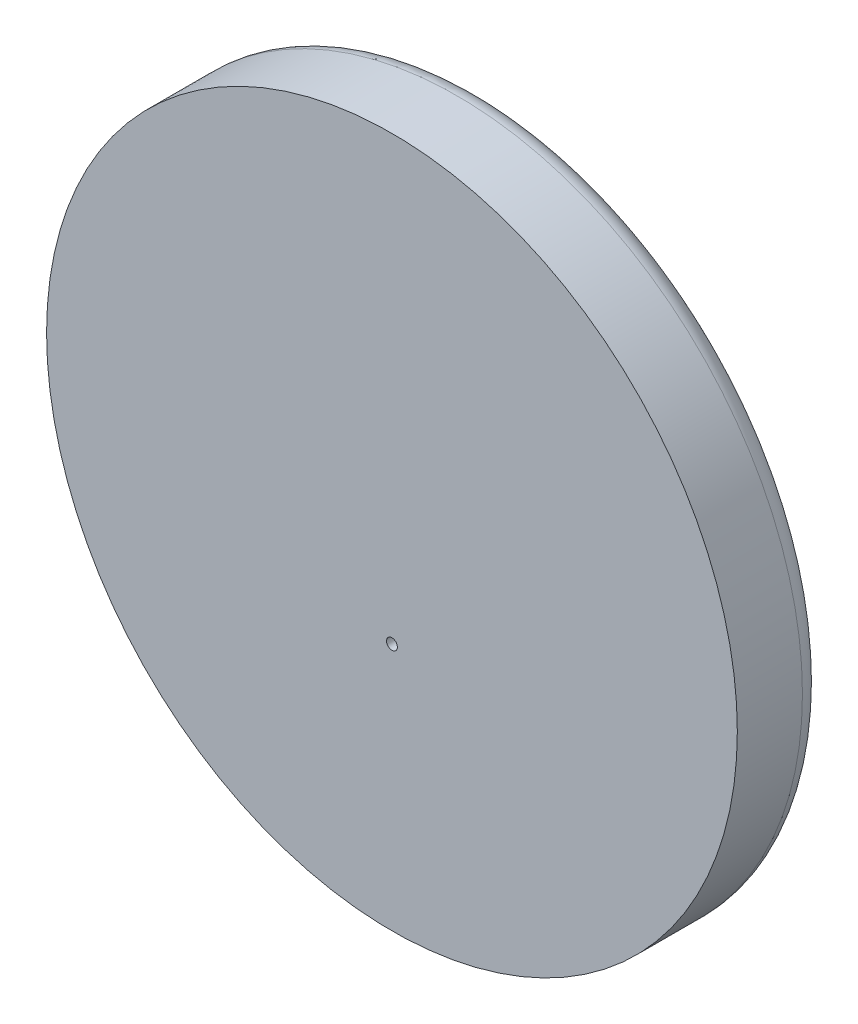
SolidWorks part; units mm, degrees
ref_plane "Front Plane" through (0, 0, 0) normal (0, 0, 1) x (1, 0, 0)
ref_plane "Top Plane" through (0, 0, 0) normal (0, 1, 0) x (1, 0, 0)
ref_plane "Right Plane" through (0, 0, 0) normal (1, 0, 0) x (0, 0, -1)
sketch "Sketch2" plane through (0, 0, 0) normal (0, 0, 1) x (1, 0, 0)
  circle A0 centre (0, 35.3882) radius 31.83
extrude "Boss-Extrude1" add sketch "Sketch2" along normal blind 8 contours A0
fillet "Fillet1" radius 2 1 edges at (31.83, 35.3882, 0)
sketch "Sketch3" plane through (0, 0, 8) normal (0, 0, 1) x (1, 0, 0)
  circle A0 centre (0, 26.4582) radius 0.5
  circle A2 centre (0, 35.3882) radius 31.83 construction
  dimension "D1" = 0
  dimension "D2" = 8.93
extrude "Cut-Extrude1" cut sketch "Sketch3" against normal through all
